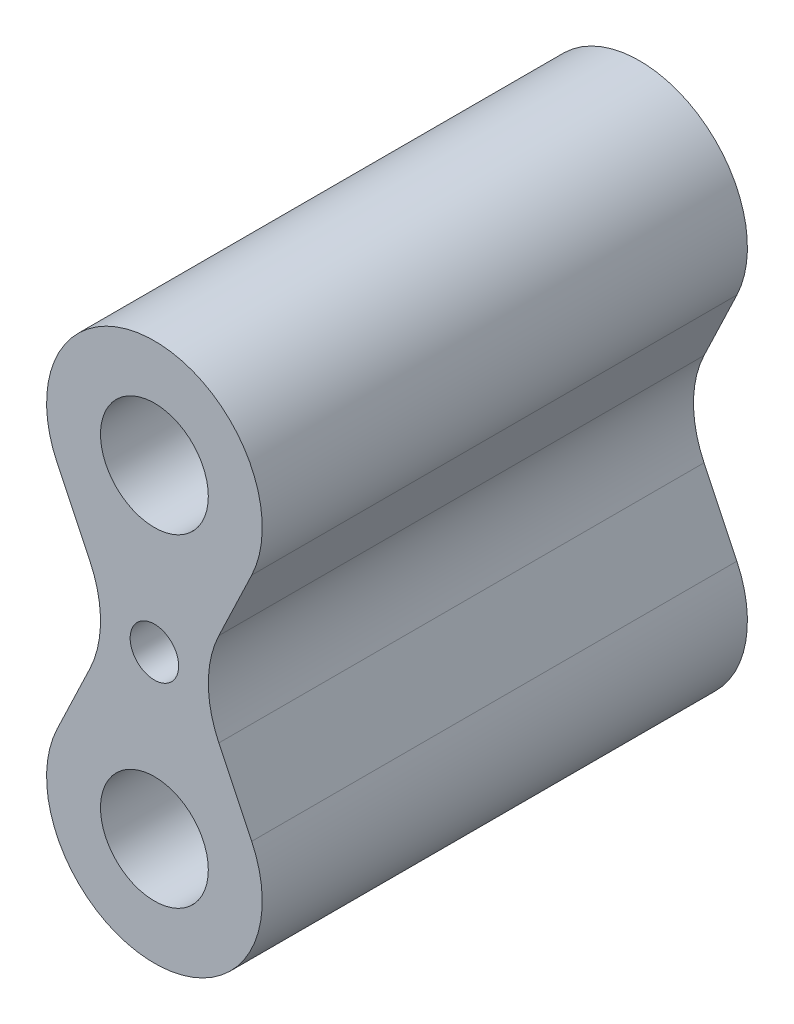
SolidWorks part; units mm, degrees
ref_plane "Front Plane" through (0, 0, 0) normal (0, 0, 1) x (1, 0, 0)
ref_plane "Top Plane" through (0, 0, 0) normal (0, 1, 0) x (1, 0, 0)
ref_plane "Right Plane" through (0, 0, 0) normal (1, 0, 0) x (0, 0, -1)
sketch "Sketch1" plane through (0, 0, 0) normal (0, 0, 1) x (1, 0, 0)
  line L0 (-18.0474, 21.3807) -> (-11.9526, 8.6193)
  line L1 (11.9526, -8.6193) -> (18.0474, -21.3807)
  line L2 (-11.9526, -8.6193) -> (-18.0474, -21.3807)
  line L3 (18.0474, 21.3807) -> (11.9526, 8.6193)
  arc A0 (-11.9526, -8.6193) -> (-11.9526, 8.6193) centre (-30, 0) ccw
  arc A1 (11.9526, 8.6193) -> (11.9526, -8.6193) centre (30, 0) ccw
  arc A2 (18.0474, 21.3807) -> (-18.0474, 21.3807) centre (0, 30) ccw
  arc A3 (-18.0474, -21.3807) -> (18.0474, -21.3807) centre (0, -30) ccw
  circle A4 centre (0, 30) radius 10
  circle A5 centre (0, -30) radius 10
  dimension "D5" = 40
  dimension "D6" = 40
  dimension "D7" = 20
  dimension "D1" = 30
  dimension "D2" = 30
  dimension "D3" = 30
  dimension "D4" = 30
extrude "Boss-Extrude1" add sketch "Sketch1" along normal mid plane 90
hole_wizard "M10x1.0 Tapped Hole1" positions "Sketch2" profile "Sketch3" tap size "M10x1.0" standard "ANSI Metric" end condition through all
sketch "Sketch2" plane through (0, 0, 45) normal (0, 0, 1) x (1, 0, 0)
  point P0 (0, 0)
sketch "Sketch3" plane through (0, 0, 45) normal (1, 0, 0) x (0, -1, 0)
  line L0 (0, 0) -> (0, 90)
  line L1 (0, 90) -> (4.5, 90)
  line L2 (4.5, 90) -> (4.5, 0)
  line L5 (4.5, 0) -> (0, 0)
  line L11 (0, -6.35) -> (0, 107.95) construction
  dimension "Thru Tap Drill Dia." = 9
  dimension "Thru Tap Drill Depth" = 90
cosmetic thread "Hole Thread1"
equation "\"Outer End Diameter\"= 40mm"
equation "\"Outer End Offset\"= \"Outer End Diameter\" * 3 / 4"
equation "\"Outer Negative Offset\"= \"Outer End Diameter\" * 3 / 4"
equation "\"D2@Sketch1\"=\"Outer End Offset\""
equation "\"D3@Sketch1\"=\"Outer Negative Offset\""
equation "\"D4@Sketch1\"=\"Outer Negative Offset\""
equation "\"D5@Sketch1\"=\"Outer End Diameter\""
equation "\"D6@Sketch1\"=\"Outer End Diameter\""
equation "\"D1@Sketch1\"=\"Outer End Offset\""
equation "\"Inner Lobe Thin Feature\"= \"Outer End Diameter\" / 2"
equation "\"D7@Sketch1\"=\"Inner Lobe Thin Feature\""
equation "\"Lobe Extrude Length\"= 90mm"
equation "\"D1@Boss-Extrude1\"=\"Lobe Extrude Length\""
